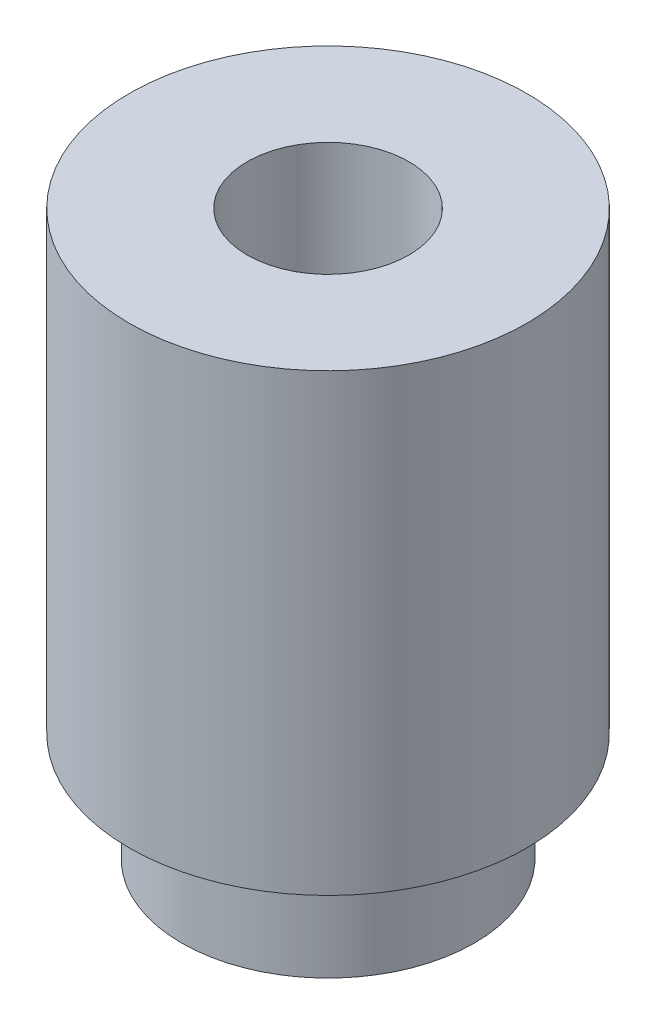
SolidWorks part; units mm, degrees
ref_plane "Front Plane" through (0, 0, 0) normal (0, 0, 1) x (1, 0, 0)
ref_plane "Top Plane" through (0, 0, 0) normal (0, 1, 0) x (1, 0, 0)
ref_plane "Right Plane" through (0, 0, 0) normal (1, 0, 0) x (0, 0, -1)
sketch "Sketch1" plane through (0, 0, 0) normal (0, 1, 0) x (1, 0, 0)
  circle A0 centre (0, 0) radius 2.045
  dimension "D1" = 4.09
extrude "Boss-Extrude1" add sketch "Sketch1" along normal blind 1.52
sketch "Sketch2" plane through (0, 1.52, 0) normal (0, 1, 0) x (1, 0, 0)
  circle A0 centre (0, 0) radius 2.78
  dimension "D1" = 5.56
extrude "Boss-Extrude2" add sketch "Sketch2" along normal blind 6.35
hole_wizard "#4-40 Tapped Hole1" positions "Sketch3" profile "Sketch5" tap size "#4-40" standard "ANSI Inch" end condition through all
sketch "Sketch3" plane through (0, 7.87, 0) normal (0, 1, 0) x (1, 0, 0)
  point P0 (0, 0)
sketch "Sketch5" plane through (0, 7.87, 0) normal (1, 0, 0) x (0, 0, 1)
  line L0 (0, 0) -> (0, 7.87)
  line L1 (0, 7.87) -> (1.1303, 7.87)
  line L2 (1.1303, 7.87) -> (1.1303, 0)
  line L5 (1.1303, 0) -> (0, 0)
  line L11 (0, -6.35) -> (0, 107.95) construction
  dimension "Thru Tap Drill Dia." = 2.2606
  dimension "Thru Tap Drill Depth" = 7.87
cosmetic thread "Hole Thread1" parameters "D2"=2.8448
